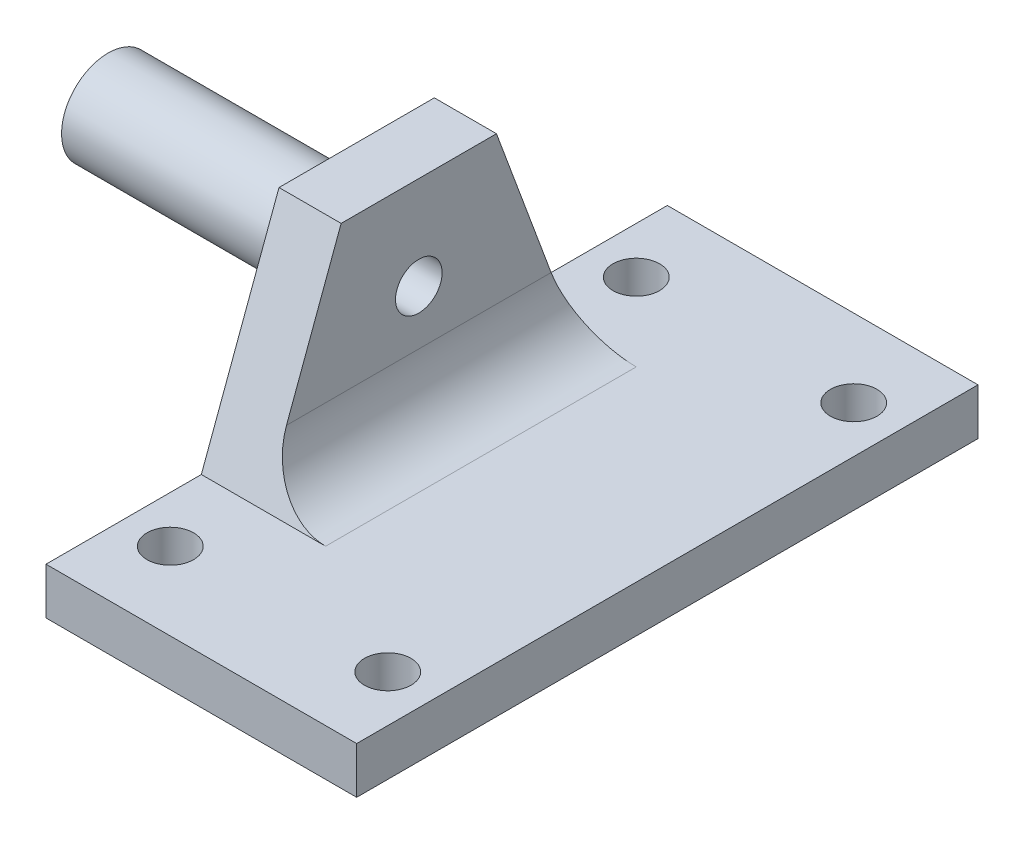
SolidWorks part; units mm, degrees
ref_plane "Front Plane" through (0, 0, 0) normal (0, 0, 1) x (1, 0, 0)
ref_plane "Top Plane" through (0, 0, 0) normal (0, 1, 0) x (1, 0, 0)
ref_plane "Right Plane" through (0, 0, 0) normal (1, 0, 0) x (0, 0, -1)
sketch "Sketch2" plane through (0, 0, 0) normal (1, 0, 0) x (0, 0, -1)
  line L0 (-10, 1.5) -> (-5, 15)
  line L1 (-20, -1.5) -> (20, -1.5)
  line L2 (-20, -1.5) -> (-20, 1.5)
  line L3 (-20, 1.5) -> (20, 1.5)
  line L4 (20, -1.5) -> (20, 1.5)
  line L5 (-20, -1.5) -> (20, 1.5) construction
  line L6 (-20, 1.5) -> (20, -1.5) construction
  line L7 (0, -1.5) -> (0, 15.1098) construction
  line L8 (-5, 15) -> (5, 15)
  line L9 (10, 1.5) -> (5, 15)
  point P0 (0, 0)
  point P12 (0, 15)
  dimension "D1" = 3
  dimension "D2" = 40
  dimension "D3" = 10
  dimension "D4" = 5
  dimension "D5" = 13.5
extrude "Boss-Extrude1" add sketch "Sketch2" along normal blind 4 contours L3 L9 L8 L0 | L1 L4 L3 L2
sketch "Sketch3" plane through (4, 0, 0) normal (1, 0, 0) x (0, 0, -1)
  line L0 (-20, -1.5) -> (-20, 1.5)
  line L1 (-20, 1.5) -> (20, 1.5)
  line L2 (20, 1.5) -> (20, -1.5)
  line L3 (20, -1.5) -> (-20, -1.5)
extrude "Boss-Extrude2" add sketch "Sketch3" along normal blind 16 contours L3 L0 L1 L2
sketch "Sketch4" plane through (0, 0, 0) normal (-1, 0, 0) x (0, 0, 1)
  line L0 (0, 15) -> (0, -1.5) construction
  line L1 (5, 15) -> (-5, 15) construction
  line L2 (20, -1.5) -> (-20, -1.5) construction
  circle A0 centre (0, 9) radius 3
  dimension "D1" = 6
  dimension "D2" = 10.5
extrude "Boss-Extrude3" add sketch "Sketch4" along normal blind 16
sketch "Sketch5" plane through (-16, 0, 0) normal (-1, 0, 0) x (0, 0, 1)
  circle A0 centre (0, 9) radius 1.5
  dimension "D1" = 3
extrude "Cut-Extrude1" cut sketch "Sketch5" against normal through all
sketch "Sketch6" plane through (0, 1.5, 0) normal (0, 1, 0) x (1, 0, 0)
  line L0 (0, 20) -> (20, -20) construction
  line L1 (3, 15) -> (17, 15)
  line L2 (3, 15) -> (3, -15)
  line L3 (3, -15) -> (17, -15)
  line L4 (17, 15) -> (17, -15)
  line L5 (3, 15) -> (17, -15) construction
  line L6 (3, -15) -> (17, 15) construction
  line L7 (20, 20) -> (0, -20) construction
  circle A0 centre (3, 15) radius 1.5
  circle A1 centre (17, 15) radius 1.5
  circle A2 centre (17, -15) radius 1.5
  circle A3 centre (3, -15) radius 1.5
  point P0 (10, 0)
  point P13 (10, 0)
  dimension "D3" = 3
  dimension "D4" = 3
  dimension "D5" = 3
  dimension "D6" = 3
  dimension "D1" = 14
  dimension "D2" = 30
extrude "Cut-Extrude2" cut sketch "Sketch6" against normal through all contours L1 A1 L4 | L4 A1 L1 | L3 A2 L4 | L4 A2 L3 | L2 A3 L3 | L3 A3 L2 | A0
ref_plane "Plane4" through (4, 1.5, 10) normal (0, 0, -1) x (-1, 0, 0)
fillet "Fillet1" radius 4 1 edges at (4, 1.5, 0)
fillet "Fillet2" radius 2 1 edges at (0, 9, -3)
